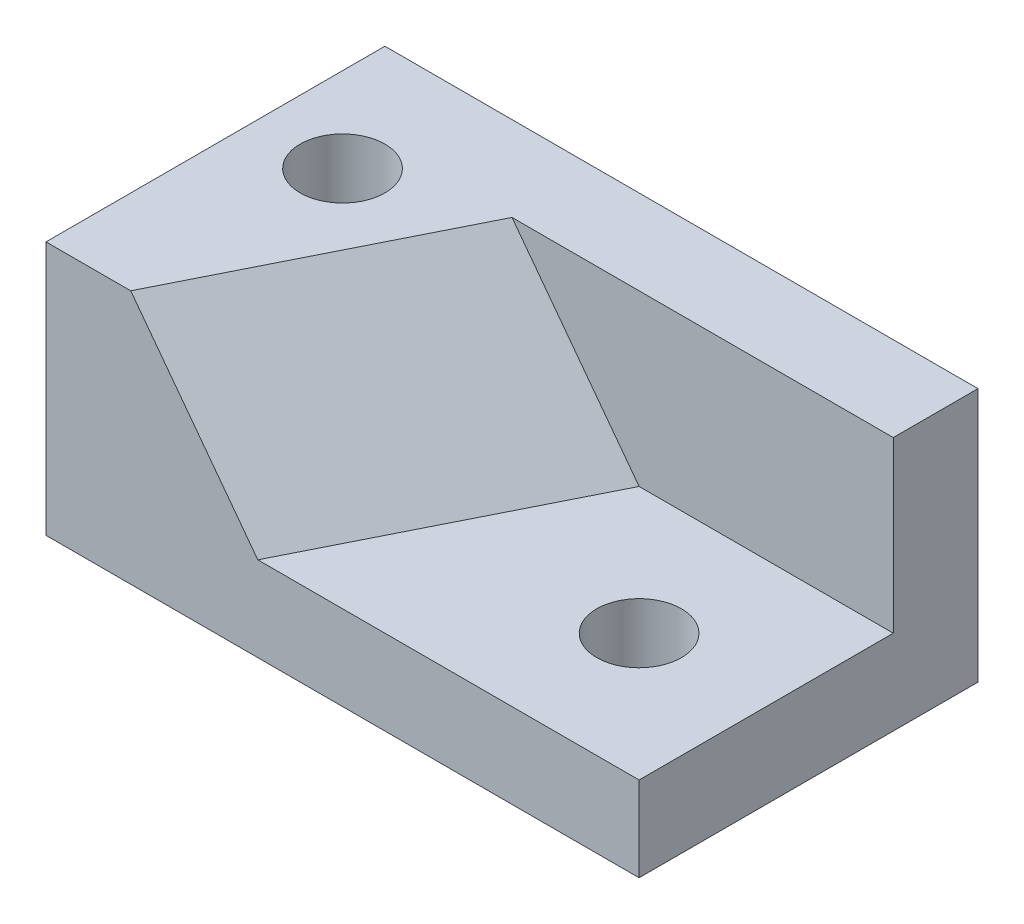
SolidWorks part; units mm, degrees
ref_plane "Front Plane" through (0, 0, 0) normal (0, 0, 1) x (1, 0, 0)
ref_plane "Top Plane" through (0, 0, 0) normal (0, 1, 0) x (1, 0, 0)
ref_plane "Right Plane" through (0, 0, 0) normal (1, 0, 0) x (0, 0, -1)
sketch "Sketch1" plane through (0, 0, 0) normal (0, 1, 0) x (1, 0, 0)
  line L1 (0, 0) -> (70, 0)
  line L2 (0, 0) -> (0, 40)
  line L3 (0, 40) -> (70, 40)
  line L4 (70, 0) -> (70, 40)
  dimension "D1" = 70
  dimension "D2" = 40
extrude "Boss-Extrude1" add sketch "Sketch1" along normal blind 30
sketch "Sketch2" plane through (0, 0, 0) normal (0, 0, 1) x (1, 0, 0)
  line L1 (70, 30) -> (40, 30)
  line L2 (70, 30) -> (70, 10)
  line L3 (70, 10) -> (40, 10)
  line L4 (40, 30) -> (40, 10)
  dimension "D1" = 30
  dimension "D2" = 20
extrude "Cut-Extrude1" cut sketch "Sketch2" against normal blind 30
sketch "Sketch3" plane through (0, 30, 0) normal (0, 1, 0) x (1, 0, 0)
  line L0 (40, 0) -> (10, 0) construction
  line L1 (0, 0) -> (40, 0) construction
  line L2 (0, 40) -> (0, 30) construction
  line L3 (0, 40) -> (0, 0) construction
  line L4 (0, 30) -> (25, 30) construction
  line L5 (10, 0) -> (25, 30)
  dimension "D1" = 30
  dimension "D2" = 10
  dimension "D3" = 25
sketch "Sketch4" plane through (0, 0, -30) normal (0, 0, 1) x (1, 0, 0)
  line L0 (25, 30) -> (40, 10)
sketch "Sketch5" plane through (0, 0, 0) normal (0, 0, 1) x (1, 0, 0)
  line L0 (0, 0) -> (0, 10) construction
  line L1 (0, 30) -> (0, 0) construction
  line L2 (0, 10) -> (25, 10) construction
  line L3 (10, 30) -> (25, 10)
  line L4 (40, 9.1016) -> (40, 10)
  dimension "D1" = 10
  dimension "D2" = 25
ref_plane "Plane1" through (17.931, 13.4483, 8.9655) normal (0.7428, 0.5571, 0.3714) x (0.2971, 0.2228, -0.9285)
sketch "Sketch8" plane through (17.931, 13.4483, 8.9655) normal (0.7428, 0.5571, 0.3714) x (0.2971, 0.2228, -0.9285)
  line L0 (9.6562, 18) -> (9.6562, -7)
  line L1 (9.6562, -7) -> (41.9671, -16)
  line L2 (41.9671, -16) -> (41.9671, 9)
  line L3 (41.9671, 9) -> (9.6562, 18)
extrude "Cut-Extrude2" cut sketch "Sketch8" along normal blind 36 contours L3 L0 L1 L2
sketch "Sketch9" plane through (0, 0, -30) normal (0, 0, 1) x (1, 0, 0)
  line L0 (25, 30) -> (40, 10)
  line L1 (40, 10) -> (40, 30)
  line L2 (40, 30) -> (25, 30)
extrude "Cut-Extrude3" cut sketch "Sketch9" along normal blind 49
sketch "Sketch10" plane through (0, 10, 0) normal (0, 1, 0) x (1, 0, 0)
  line L0 (25, 0) -> (40, 0)
  line L1 (40, 0) -> (40, 30)
  line L2 (40, 30) -> (25, 0)
extrude "Cut-Extrude5" cut sketch "Sketch10" along normal blind 21
sketch "Sketch11" plane through (0, 10, 0) normal (0, 1, 0) x (1, 0, 0)
  line L0 (70, 0) -> (70, 15) construction
  line L1 (70, 30) -> (70, 0) construction
  line L2 (70, 15) -> (55, 15) construction
  circle A0 centre (55, 15) radius 5
  dimension "D1" = 15
extrude "Cut-Extrude6" cut sketch "Sketch11" against normal through all
sketch "Sketch12" plane through (0, 30, 0) normal (0, 1, 0) x (1, 0, 0)
  line L0 (0, 40) -> (0, 25) construction
  line L1 (0, 40) -> (0, 0) construction
  line L2 (0, 25) -> (10, 25) construction
  circle A0 centre (10, 25) radius 5
  dimension "D1" = 15
  dimension "D2" = 10
extrude "Cut-Extrude7" cut sketch "Sketch12" against normal through all
